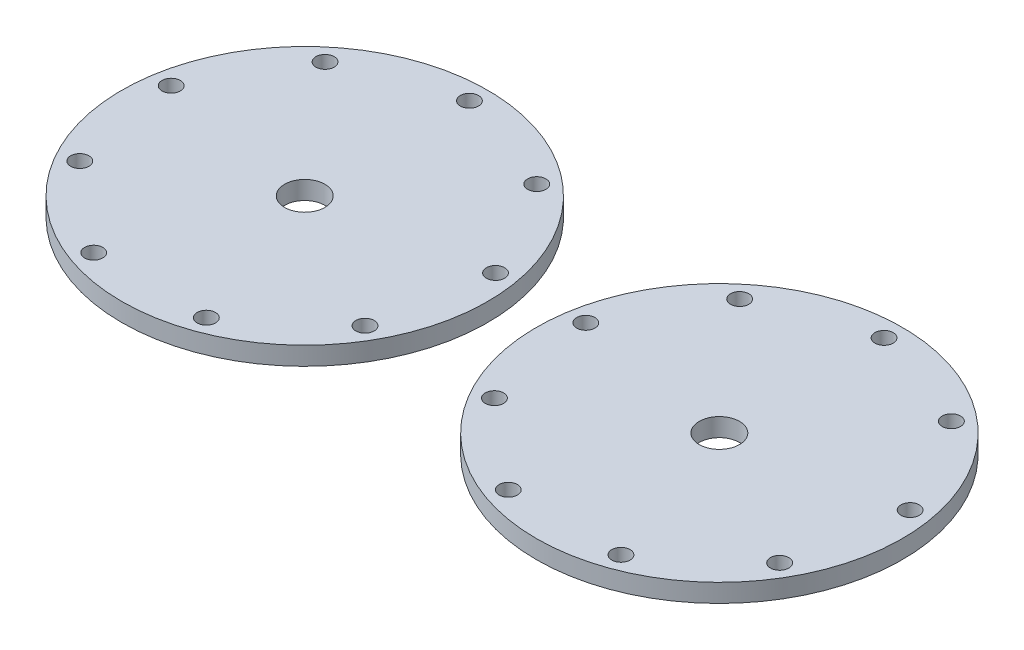
SolidWorks part; units mm, degrees
ref_plane "前视基准面" through (0, 0, 0) normal (0, 0, 1) x (1, 0, 0)
ref_plane "上视基准面" through (0, 0, 0) normal (0, 1, 0) x (1, 0, 0)
ref_plane "右视基准面" through (0, 0, 0) normal (1, 0, 0) x (0, 0, -1)
other "Configuration Table"
sketch "草图1" plane through (0, 0, 0) normal (0, 1, 0) x (1, 0, 0)
  line L0 (0, 54) -> (0, 0) construction
  line L1 (-135.319, 53.3568) -> (-135.319, -0.6432) construction
  circle A0 centre (0, 0) radius 60
  circle A1 centre (0, 54) radius 3
  circle A10 centre (0, 0) radius 6.6
  circle A16 centre (34.7105, 41.3664) radius 3
  circle A17 centre (53.1796, 9.377) radius 3
  circle A18 centre (46.7654, -27) radius 3
  circle A19 centre (18.4691, -50.7434) radius 3
  circle A20 centre (-18.4691, -50.7434) radius 3
  circle A21 centre (-46.7654, -27) radius 3
  circle A22 centre (-53.1796, 9.377) radius 3
  circle A23 centre (-34.7105, 41.3664) radius 3
  circle A24 centre (-135.319, -0.6432) radius 60
  circle A25 centre (-135.319, 53.3568) radius 3
  circle A26 centre (-135.319, -0.6432) radius 6.6
  circle A27 centre (-100.6085, 40.7232) radius 3
  circle A28 centre (-82.1394, 8.7339) radius 3
  circle A29 centre (-88.5537, -27.6432) radius 3
  circle A30 centre (-116.8499, -51.3866) radius 3
  circle A31 centre (-153.7881, -51.3866) radius 3
  circle A32 centre (-182.0844, -27.6432) radius 3
  circle A33 centre (-188.4987, 8.7339) radius 3
  circle A34 centre (-170.0296, 40.7232) radius 3
  point P25 (0, 0)
  point P44 (-135.319, -0.6432)
  dimension "D1" = 120
  dimension "D2" = 6
  dimension "D4" = 9
  dimension "D5" = 54
  dimension "D7" = 13.2
  dimension "D8" = 120
  dimension "D9" = 6
  dimension "D13" = 36.9382
  dimension "D11" = 13.2
  dimension "D3" = 54
  dimension "D6" = 36.9382
  dimension "D10" = 54
  dimension "D12" = 54
extrude "凸台-拉伸1" add sketch "草图1" along normal blind 6 contours A0
